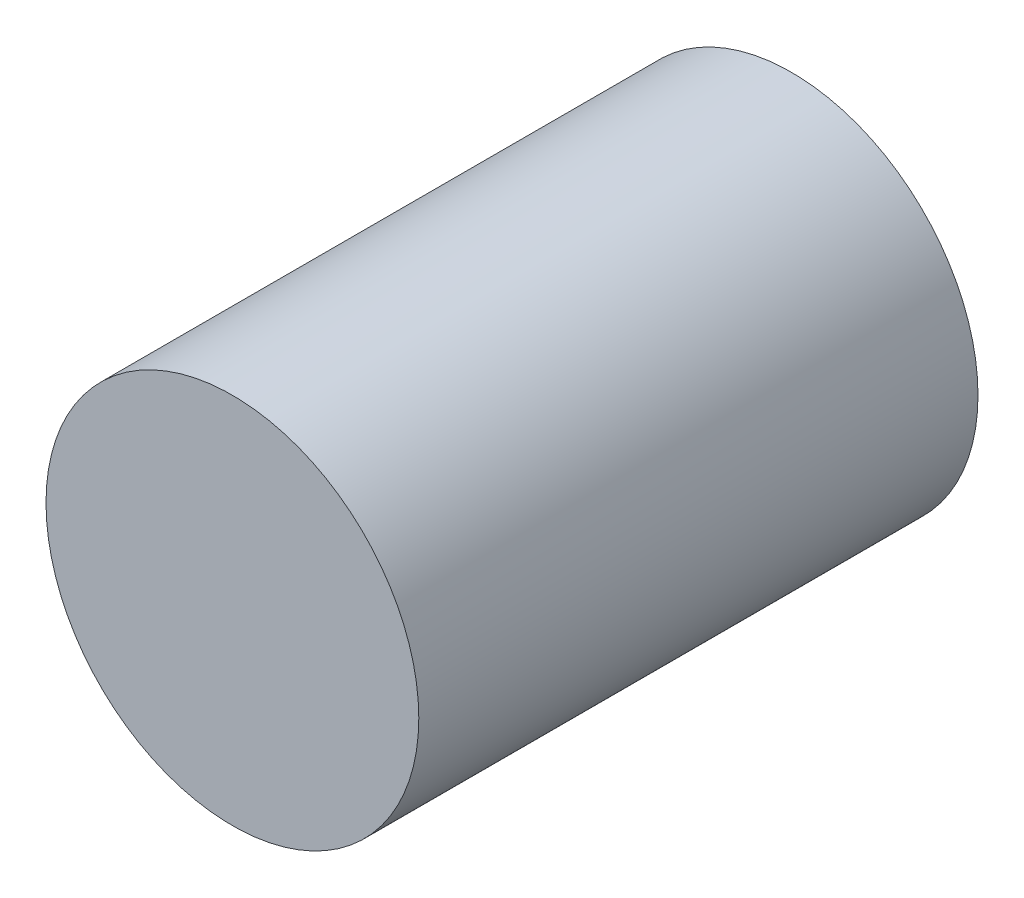
SolidWorks part; units mm, degrees
material "ABS"
ref_plane "Front Plane" through (0, 0, 0) normal (0, 0, 1) x (1, 0, 0)
ref_plane "Top Plane" through (0, 0, 0) normal (0, 1, 0) x (1, 0, 0)
ref_plane "Right Plane" through (0, 0, 0) normal (1, 0, 0) x (0, 0, -1)
sketch "Sketch1" plane through (0, 0, 0) normal (0, 0, 1) x (1, 0, 0)
  circle A0 centre (0, 0) radius 25
  dimension "D1" = 50
extrude "Boss-Extrude1" add sketch "Sketch1" along normal mid plane 75
